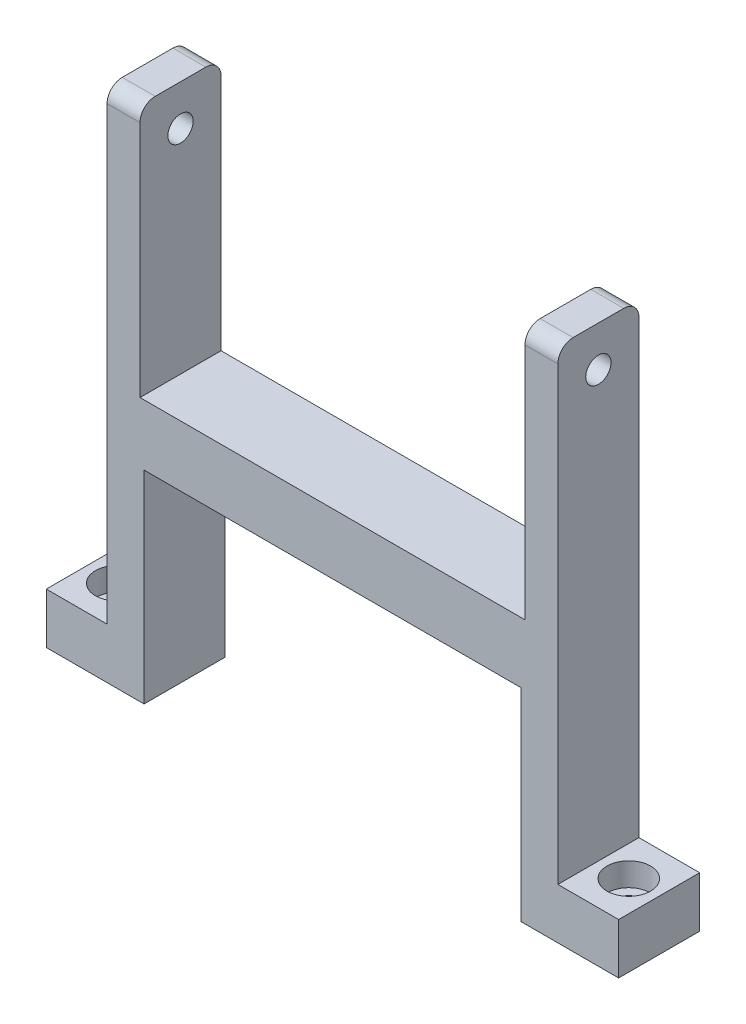
SolidWorks part; units mm, degrees
ref_plane "前视基准面" through (0, 0, 0) normal (0, 0, 1) x (1, 0, 0)
ref_plane "上视基准面" through (0, 0, 0) normal (0, 1, 0) x (1, 0, 0)
ref_plane "右视基准面" through (0, 0, 0) normal (1, 0, 0) x (0, 0, -1)
sketch "草图1" plane through (0, 0, 0) normal (0, 0, 1) x (1, 0, 0)
  line L1 (22.25, -25.5) -> (-22.25, -25.5)
  line L2 (22.25, -25.5) -> (22.25, 25.5)
  line L3 (22.25, 25.5) -> (-22.25, 25.5)
  line L4 (-22.25, -25.5) -> (-22.25, 25.5)
  line L5 (22.25, -25.5) -> (-22.25, 25.5) construction
  line L6 (22.25, 25.5) -> (-22.25, -25.5) construction
  point P0 (0, 0)
  dimension "D1" = 44.5
  dimension "D2" = 51
extrude "凸台-拉伸1" add sketch "草图1" along normal blind 8
sketch "草图2" plane through (0, 0, 8) normal (0, 0, 1) x (1, 0, 0)
  line L0 (-19, 25.5) -> (-19, 0.5)
  line L1 (22.25, 25.5) -> (-22.25, 25.5) construction
  line L2 (-19, 0.5) -> (19, 0.5)
  line L3 (19, 0.5) -> (19, 25.5)
  line L4 (19, 25.5) -> (-19, 25.5)
  dimension "D1" = 38
  dimension "D2" = 19
  dimension "D3" = 25
extrude "切除-拉伸1" cut sketch "草图2" against normal through all
hole_wizard "大小mm 暗销孔1" positions "草图3" profile "草图4" hole size "Ø2.5" standard "GB" end condition through all
sketch "草图3" plane through (-22.25, 0, 0) normal (-1, 0, 0) x (0, 0, 1)
  line L0 (4, 25.5) -> (4, 21.5) construction
  line L1 (8, 25.5) -> (0, 25.5) construction
  point P0 (4, 21.5)
  dimension "D1" = 4
sketch "草图4" plane through (-22.25, 21.5, 4) normal (0, 1, 0) x (0, 0, 1)
  line L0 (0, 0) -> (0, 44.5)
  line L1 (0, 44.5) -> (1.25, 44.5)
  line L2 (1.25, 44.5) -> (1.25, 0)
  line L5 (1.25, 0) -> (0, 0)
  line L11 (0, -6.35) -> (0, 107.95) construction
  dimension "通孔孔直径" = 2.5
  dimension "通孔孔深度" = 44.5
fillet "圆角1" radius 1.5 4 edges at (-20.625, 25.5, 0) (20.625, 25.5, 0) (20.625, 25.5, 8) (-20.625, 25.5, 8)
sketch "草图5" plane through (0, 0, 0) normal (0, 0, -1) x (-1, 0, 0)
  line L0 (18.6, -25.5) -> (18.6, -5.5)
  line L1 (22.25, -25.5) -> (-22.25, -25.5) construction
  line L2 (18.6, -5.5) -> (-18.6, -5.5)
  line L3 (-18.6, -5.5) -> (-18.6, -25.5)
  line L4 (-18.6, -25.5) -> (18.6, -25.5)
  line L5 (0, 0) -> (0, -3.9886) construction
  dimension "D1" = 37.2
  dimension "D2" = 18.6
  dimension "D3" = 20
extrude "切除-拉伸2" cut sketch "草图5" against normal blind 15
sketch "草图6" plane through (0, -25.5, 0) normal (0, -1, 0) x (1, 0, 0)
  line L0 (-22.25, 0) -> (-28.25, 0)
  line L1 (-28.25, 0) -> (-28.25, 8)
  line L2 (-28.25, 8) -> (-22.25, 8)
  line L3 (-22.25, 8) -> (-22.25, 0)
  dimension "D1" = 6
extrude "凸台-拉伸2" add sketch "草图6" against normal blind 5
mirror "镜向1" about plane through (0, 0, 0) normal (1, 0, 0) of "凸台-拉伸2"
hole_wizard "打孔尺寸(%根据)内六角圆柱头螺钉的类型2" positions "草图7" profile "草图8" counterbore size "M2" standard "GB" end condition through all
sketch "草图7" plane through (0, -20.5, 0) normal (0, 1, 0) x (1, 0, 0)
  line L0 (-25.25, 0) -> (-25.25, -8) construction
  line L1 (-28.25, 0) -> (-22.25, 0) construction
  line L2 (-22.25, -8) -> (-28.25, -8) construction
  point P0 (-25.25, -4)
sketch "草图8" plane through (-25.25, -20.5, 4) normal (1, 0, 0) x (0, 0, 1)
  line L0 (0, 0) -> (0, 5)
  line L1 (0, 5) -> (1.2, 5)
  line L3 (1.2, 5) -> (1.2, 2.3)
  line L4 (1.2, 2.3) -> (2.15, 2.3)
  line L5 (2.15, 2.3) -> (2.15, 0)
  line L7 (2.15, 0) -> (0, 0)
  line L11 (0, -6.35) -> (0, 107.95) construction
  dimension "通孔孔直径" = 2.4
  dimension "通孔孔深度" = 5
  dimension "柱形沉头孔直径" = 4.3
  dimension "柱形沉头孔深度" = 2.3
mirror "镜向2" about plane through (0, 0, 0) normal (1, 0, 0) of "打孔尺寸(%根据)内六角圆柱头螺钉的类型2"
